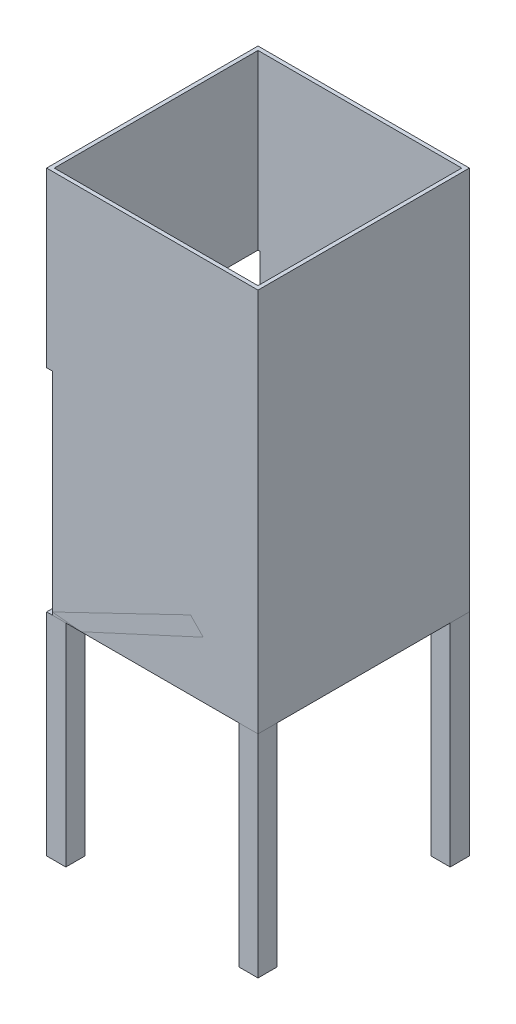
SolidWorks part; units mm, degrees
ref_plane "Front Plane" through (0, 0, 0) normal (0, 0, 1) x (1, 0, 0)
ref_plane "Top Plane" through (0, 0, 0) normal (0, 1, 0) x (1, 0, 0)
ref_plane "Right Plane" through (0, 0, 0) normal (1, 0, 0) x (0, 0, -1)
sketch "Sketch1" plane through (0, 0, 0) normal (0, 1, 0) x (1, 0, 0)
  line L1 (-55, 55) -> (55, 55)
  line L2 (-55, 55) -> (-55, -55)
  line L3 (-55, -55) -> (55, -55)
  line L4 (55, 55) -> (55, -55)
  line L5 (-55, 55) -> (55, -55) construction
  line L6 (-55, -55) -> (55, 55) construction
  point P0 (0, 0)
  dimension "D1" = 110
  dimension "D2" = 110
extrude "Boss-Extrude1" add sketch "Sketch1" along normal blind 200
shell "Shell1" thickness 2
sketch "Sketch2" plane through (0, 0, 0) normal (0, 1, 0) x (1, 0, 0)
  line L1 (55, -55) -> (45, -55)
  line L2 (55, -55) -> (55, -45)
  line L3 (55, -45) -> (45, -45)
  line L4 (45, -55) -> (45, -45)
  line L5 (55, 55) -> (45, 55)
  line L6 (55, 55) -> (55, 45)
  line L7 (55, 45) -> (45, 45)
  line L8 (45, 55) -> (45, 45)
  line L9 (-55, -55) -> (-45, -55)
  line L10 (-55, -55) -> (-55, -45)
  line L11 (-55, -45) -> (-45, -45)
  line L12 (-45, -55) -> (-45, -45)
  line L13 (-55, 55) -> (-45, 55)
  line L14 (-55, 55) -> (-55, 45)
  line L15 (-55, 45) -> (-45, 45)
  line L16 (-45, 55) -> (-45, 45)
  dimension "D1" = 10
  dimension "D2" = 10
  dimension "D3" = 10
  dimension "D4" = 10
  dimension "D5" = 10
  dimension "D6" = 10
  dimension "D7" = 10
extrude "Boss-Extrude2" add sketch "Sketch2" against normal blind 110 separate body
sketch "Sketch3" plane through (0, 0, 0) normal (0, 0, 1) x (1, 0, 0)
  line L0 (-55, 0) -> (55, 52.982)
  line L1 (55, 200) -> (55, 0) construction
  line L2 (55, 52.982) -> (55, 42.4741)
  line L3 (55, 42.4741) -> (-37.0808, 0)
  line L4 (-55, 0) -> (55, 0) construction
  line L5 (-37.0808, 0) -> (-55, 0)
extrude "Boss-Extrude3" add sketch "Sketch3" along normal blind 55 and the other way blind 55 separate body
ref_plane "Plane2" through (-55, 0, 0) normal (-1, 0, 0) x (0, 0, 1)
sketch "Sketch4" plane through (-55, 0, 0) normal (-1, 0, 0) x (0, 0, 1)
  line L0 (55, 200) -> (55, 0) construction
  line L1 (-55, 0) -> (55, 0)
  line L2 (-55, 0) -> (-55, 110)
  line L3 (-55, 110) -> (55, 110)
  line L4 (55, 0) -> (55, 110)
  line L5 (-55, 0) -> (55, 0) construction
  dimension "D1" = 110
extrude "Cut-Extrude1" cut sketch "Sketch4" against normal blind 3
